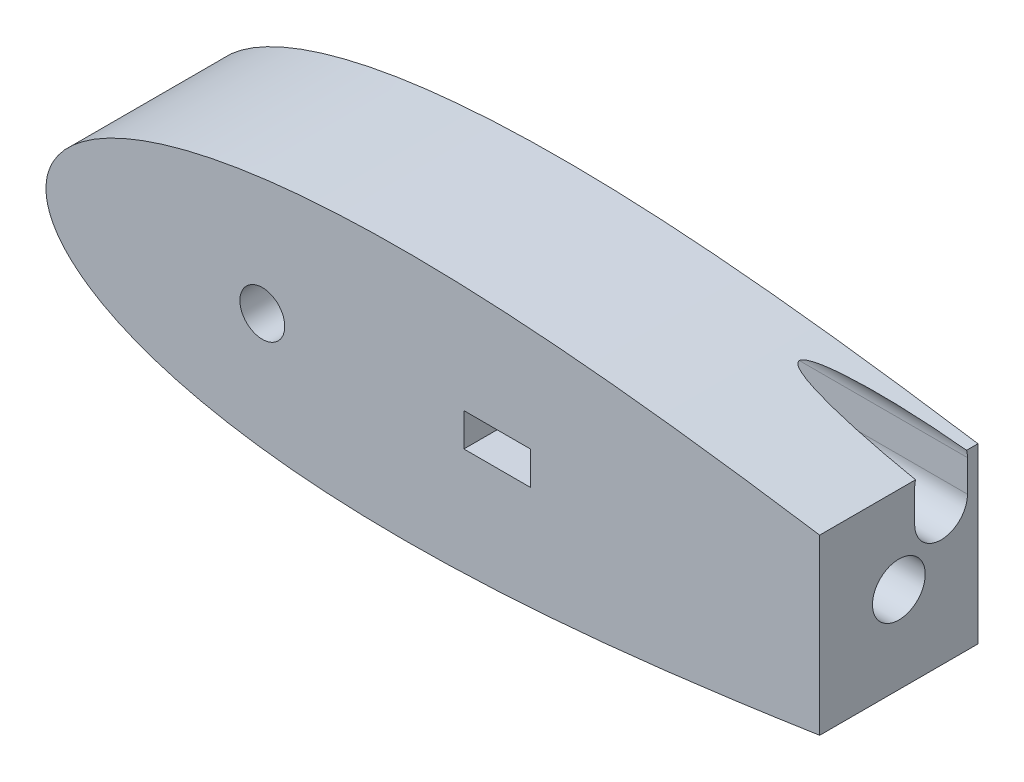
SolidWorks part; units mm, degrees
ref_plane "Front Plane" through (0, 0, 0) normal (0, 0, 1) x (1, 0, 0)
ref_plane "Top Plane" through (0, 0, 0) normal (0, 1, 0) x (1, 0, 0)
ref_plane "Right Plane" through (0, 0, 0) normal (1, 0, 0) x (0, 0, -1)
sketch "Sketch1" plane through (0, 0, 0) normal (0, 0, 1) x (1, 0, 0)
  line L0 (100, 0) -> (0, 0) construction
  line L1 (1.2169, -991.9959) -> (1.2169, 49008.0041) construction
  line L2 (93.345, 0) -> (114.935, 0) construction
  line L3 (125.634, 0) -> (131.6629, 0) construction
  line L4 (643.5991, 0) -> (643.5991, -1.016)
  line L9 (0, 0) -> (643.9668, 0)
  line L13 (460.661, 0) -> (473.361, 0)
  circle A0 centre (104.14, 0) radius 10.795 construction
  arc A1 (1.2169, -4.6585) -> (1.2169, 4.6585) centre (9.525, 0) cw
  arc A2 (641.5671, 0) -> (644.1071, 0) centre (642.8371, 0) ccw
  circle A4 centre (104.14, 0) radius 10.795
  circle A9 centre (40.64, 0) radius 12.7
  circle A14 centre (642.3793, 0) radius 1.5875 construction
  arc A15 (642.5108, -1.582) -> (642.5108, 1.582) centre (642.3793, 0) ccw
  spline S2 degree 3 poles (666.3448, -0.0547) (672.2538, 0) (666.3448, 0.0547) (662.8509, 0.2344) (656.505, 0.5436) (649.293, 1.0348) (640.4916, 1.7319) (630.4138, 2.6634) (619.0141, 3.8493) (606.375, 5.3044) (592.5439, 7.0376) (577.5855, 9.0506) (561.5643, 11.3389) (544.5497, 13.8907) (526.6141, 16.6877) (507.8326, 19.7051) (488.2827, 22.9117) (468.0444, 26.2704) (447.1994, 29.739) (425.8316, 33.2703) (404.0263, 36.8132) (381.8707, 40.3133) (359.4533, 43.7135) (336.8645, 46.9554) (314.1962, 49.9798) (291.5418, 52.7277) (268.9963, 55.1412) (246.6566, 57.1646) (224.6209, 58.7452) (202.9892, 59.8341) (181.8631, 60.3875) (161.3458, 60.367) (141.542, 59.7399) (122.5581, 58.4818) (104.5023, 56.5743) (87.485, 54.0089) (71.6197, 50.7848) (57.0237, 46.9125) (43.8205, 42.415) (32.1416, 37.3322) (22.1291, 31.7315) (13.9324, 25.7264) (7.6896, 19.5132) (3.4631, 13.4204) (1.1063, 7.9234) (0.1546, 3.5138) (-0.0622, 0) (0.1546, -3.5138) (1.1063, -7.9234) (3.4631, -13.4204) (7.6896, -19.5132) (13.9324, -25.7264) (22.1291, -31.7315) (32.1416, -37.3322) (43.8205, -42.415) (57.0237, -46.9125) (71.6197, -50.7848) (87.485, -54.0089) (104.5023, -56.5743) (122.5581, -58.4818) (141.542, -59.7399) (161.3458, -60.367) (181.8631, -60.3875) (202.9892, -59.8341) (224.6209, -58.7452) (246.6566, -57.1646) (268.9963, -55.1412) (291.5418, -52.7277) (314.1962, -49.9798) (336.8645, -46.9554) (359.4533, -43.7135) (381.8707, -40.3133) (404.0263, -36.8132) (425.8316, -33.2703) (447.1994, -29.739) (468.0444, -26.2704) (488.2827, -22.9117) (507.8326, -19.7051) (526.6141, -16.6877) (544.5497, -13.8907) (561.5643, -11.3389) (577.5855, -9.0506) (592.5439, -7.0376) (606.375, -5.3044) (619.0141, -3.8493) (630.4138, -2.6634) (640.4916, -1.7319) (649.293, -1.0348) (656.505, -0.5436) (662.8509, -0.2344) (666.3448, -0.0547) (672.2538, 0) (666.3448, 0.0547) knots -0.009667 -0.005395 -0.002168 0 0.002168 0.005395 0.009667 0.014967 0.021271 0.028553 0.036781 0.04592 0.055932 0.066773 0.078397 0.090755 0.103793 0.117456 0.131686 0.146422 0.1616 0.177156 0.193024 0.209135 0.225421 0.241812 0.258238 0.274629 0.290914 0.307025 0.322893 0.338448 0.353626 0.368361 0.38259 0.396253 0.40929 0.421647 0.43327 0.444109 0.454119 0.463255 0.471479 0.478755 0.485052 0.490344 0.49461 0.497833 0.5 0.502167 0.50539 0.509656 0.514948 0.521245 0.528521 0.536745 0.545881 0.555891 0.56673 0.578353 0.59071 0.603747 0.61741 0.631639 0.646374 0.661552 0.677107 0.692975 0.709086 0.725371 0.741762 0.758188 0.774579 0.790865 0.806976 0.822844 0.8384 0.853578 0.868314 0.882544 0.896207 0.909245 0.921603 0.933227 0.944068 0.95408 0.963219 0.971447 0.978729 0.985033 0.990333 0.994605 0.997832 1 1.002168 1.005395 1.009667 only from (670.56, 0) to (670.56, 0)
  point P2 (167.64, 0)
  point P8 (1.2169, -4.6585)
  point P10 (1.2169, 4.6585)
  point P28 (133.9182, 0)
  point P49 (130.0977, 0)
  point P59 (95.1064, 0)
  dimension "D2" = 21.59
  dimension "D3" = 1.016
  dimension "D4" = 1.27
  dimension "D8" = 25.4
  dimension "D9" = 63.5
  dimension "D10" = 3.175
  dimension "D6" = 63.5
extrude "Boss-Extrude1" add sketch "Sketch1" along normal blind 76.2 contours S2
sketch "Sketch3" plane through (0, 0, 76.2) normal (0, 0, 1) x (1, 0, 0)
  circle A0 centre (104.1392, 0) radius 10.795
  dimension "D1" = 21.59
extrude "Cut-Extrude2" cut sketch "Sketch3" against normal blind 76.2
sketch "Sketch4" plane through (0, 0, 76.2) normal (0, 0, 1) x (1, 0, 0)
sketch "Sketch6" plane through (0, 0, 0) normal (1, 0, 0) x (0, 0, -1)
  circle A0 centre (-20.32, 0) radius 6.35
  dimension "D1" = 12.7
  dimension "D2" = 20.32
extrude "Cut-Extrude3" cut sketch "Sketch6" against normal blind 0.0003 and the other way blind 53.34
sketch "Sketch7" plane through (0, 0, 0) normal (0, 0, -1) x (-1, 0, 0)
  circle A0 centre (-38.1, 0) radius 1.5875
  circle A1 centre (-50.8, 0) radius 1.5875
  dimension "D1" = 3.175
  dimension "D2" = 3.175
  dimension "D3" = 12.7
  dimension "D4" = 38.1
extrude "Cut-Extrude4" cut sketch "Sketch7" against normal blind 30.48
sketch "Sketch8" plane through (0, 0, 0) normal (0, 0, -1) x (-1, 0, 0)
  line L1 (-677.2433, 63.9901) -> (-372.4433, 63.9901)
  line L2 (-677.2433, 63.9901) -> (-677.2433, -63.0099)
  line L3 (-677.2433, -63.0099) -> (-372.4433, -63.0099)
  line L4 (-372.4433, 63.9901) -> (-372.4433, -63.0099)
  dimension "D1" = 127
  dimension "D2" = 372.4433
  dimension "D3" = 304.8
extrude "Cut-Extrude5" cut sketch "Sketch8" against normal blind 76.2
sketch "Sketch9" plane through (372.4433, 0, 0) normal (1, 0, 0) x (0, 0, -1)
  line L0 (0, -41.7363) -> (0, 41.7363) construction
  circle A0 centre (-38.1, 0) radius 12.7
  dimension "D1" = 25.4
  dimension "D2" = 38.1
extrude "Cut-Extrude6" cut sketch "Sketch9" against normal blind 101.6 contours A0
sketch "Sketch10" plane through (0, 0, 0) normal (0, 0, -1) x (-1, 0, 0)
  line L0 (-372.4433, -41.7363) -> (-372.4433, 41.7363) construction
  circle A0 centre (-343.8683, 0) radius 3.175
  circle A1 centre (-286.7183, 0) radius 3.175
  dimension "D1" = 57.15
  dimension "D2" = 28.575
  dimension "D3" = 6.35
  dimension "D4" = 6.35
extrude "Cut-Extrude7" cut sketch "Sketch10" against normal blind 57.15
sketch "Sketch11" plane through (0, 0, 0) normal (0, 0, -1) x (-1, 0, 0)
  circle A0 centre (-286.7183, 0) radius 5.08
  circle A1 centre (-343.8683, 0) radius 5.08
  dimension "D1" = 10.16
extrude "Cut-Extrude8" cut sketch "Sketch11" against normal blind 6.35
sketch "Sketch12" plane through (0, 0, 0) normal (0, 0, -1) x (-1, 0, 0)
  circle A0 centre (-38.1, 0) radius 3.175
  circle A1 centre (-50.8, 0) radius 3.175
  dimension "D1" = 6.35
  dimension "D2" = 6.35
extrude "Cut-Extrude9" cut sketch "Sketch12" against normal blind 6.35
sketch "Sketch13" plane through (372.4433, 0, 0) normal (1, 0, 0) x (0, 0, -1)
  line L0 (-17.78, 23.2323) -> (-17.78, 38.4723) construction
  line L1 (-30.48, 23.2323) -> (-30.48, 38.4723)
  line L2 (-5.08, 23.2323) -> (-5.08, 38.4723)
  line L3 (0, -41.7363) -> (0, 41.7363) construction
  line L4 (-76.2, -41.7363) -> (-76.2, 41.7363) construction
  arc A0 (-30.48, 23.2323) -> (-5.08, 23.2323) centre (-17.78, 23.2323) ccw
  arc A1 (-5.08, 38.4723) -> (-30.48, 38.4723) centre (-17.78, 38.4723) ccw
  point P2 (-17.78, 30.8523)
  dimension "D1" = 5.08
  dimension "D2" = 45.72
  dimension "D4" = 15.24
extrude "Cut-Extrude10" cut sketch "Sketch13" against normal blind 198.458
sketch "Sketch15" plane through (0, 0, 0) normal (0, 0, -1) x (-1, 0, 0)
  line L0 (-372.4433, -41.7363) -> (-372.4433, 41.7363) construction
  line L1 (-261.3613, -30.48) -> (-173.9853, -30.48)
  line L2 (-261.3613, -30.48) -> (-261.3613, 30.48)
  line L3 (-261.3613, 30.48) -> (-173.9853, 30.48)
  line L4 (-173.9853, -30.48) -> (-173.9853, 30.48)
  point P4 (0, 0)
  point P5 (0, 0)
  point P6 (0, 0)
  point P7 (0, 0)
  dimension "D1" = 87.376
  dimension "D2" = 60.96
  dimension "D3" = 111.082
extrude "Cut-Extrude11" cut sketch "Sketch15" against normal blind 33.3
sketch "Sketch17" plane through (0, 0, 33.3) normal (0, 0, -1) x (-1, 0, 0)
  line L0 (-173.9853, -30.48) -> (-173.9853, 30.48) construction
  line L1 (-233.1711, 8) -> (-201.1711, 8)
  line L2 (-233.1711, 8) -> (-233.1711, -8)
  line L3 (-233.1711, -8) -> (-201.1711, -8)
  line L4 (-201.1711, 8) -> (-201.1711, -8)
  line L5 (-173.9853, 30.48) -> (-261.3613, 30.48) construction
  dimension "D1" = 27.1858
  dimension "D2" = 32
  dimension "D3" = 16
  dimension "D4" = 22.48
extrude "Cut-Extrude12" cut sketch "Sketch17" against normal blind 50.8
sketch "Sketch18" plane through (0, 0, 33.3) normal (0, 0, -1) x (-1, 0, 0)
  line L0 (-233.1711, 8) -> (-233.1711, -8) construction
  line L1 (-201.1711, -8) -> (-201.1711, 8) construction
  circle A0 centre (-199.4711, 0) radius 1.5
  circle A1 centre (-234.8711, 0) radius 1.5
  point P6 (-233.1711, 0)
  point P7 (0, 0)
  dimension "D1" = 3
  dimension "D2" = 3
  dimension "D3" = 1.7
  dimension "D4" = 1.7
extrude "Cut-Extrude13" cut sketch "Sketch18" against normal blind 25.4
sketch "Sketch19" plane through (0, 0, 0) normal (0, 0, -1) x (-1, 0, 0)
  line L1 (-166.0439, 28.3517) -> (-112.7039, 28.3517)
  line L2 (-166.0439, 28.3517) -> (-166.0439, 49.9417)
  line L3 (-166.0439, 49.9417) -> (-112.7039, 49.9417)
  line L4 (-112.7039, 28.3517) -> (-112.7039, 49.9417)
  dimension "D1" = 53.34
  dimension "D2" = 21.59
extrude "Cut-Extrude14" cut sketch "Sketch19" against normal blind 66.04
sketch "Sketch21" plane through (0, 0, 0) normal (0, 0, -1) x (-1, 0, 0)
  line L0 (-166.0439, 28.3517) -> (-112.7039, 28.3517) construction
  line L1 (-153.594, 10.3217) -> (-125.154, 10.3217)
  line L2 (-153.594, 10.3217) -> (-153.594, 24.5417)
  line L3 (-153.594, 24.5417) -> (-125.154, 24.5417)
  line L4 (-125.154, 10.3217) -> (-125.154, 24.5417)
  point P4 (0, 0)
  point P6 (0, 0)
  dimension "D1" = 28.44
  dimension "D2" = 14.22
  dimension "D3" = 3.81
  dimension "D4" = 13.02
extrude "Cut-Extrude15" cut sketch "Sketch21" against normal blind 50.8
sketch "Sketch23" plane through (0, 0, 0) normal (0, 0, -1) x (-1, 0, 0)
  line L0 (-153.594, 24.5417) -> (-153.594, 10.3217) construction
  line L1 (-155.372, 8.2897) -> (-123.376, 8.2897)
  line L2 (-155.372, 8.2897) -> (-155.372, 26.5737)
  line L3 (-155.372, 26.5737) -> (-123.376, 26.5737)
  line L4 (-123.376, 8.2897) -> (-123.376, 26.5737)
  line L5 (-125.154, 10.3217) -> (-125.154, 24.5417) construction
  line L6 (-153.594, 10.3217) -> (-125.154, 10.3217) construction
  line L7 (-125.154, 24.5417) -> (-153.594, 24.5417) construction
  dimension "D1" = 1.778
  dimension "D2" = 1.778
  dimension "D3" = 2.032
  dimension "D4" = 2.032
extrude "Cut-Extrude16" cut sketch "Sketch23" against normal blind 10.16
sketch "Sketch24" plane through (0, 0, 0) normal (0, 0, -1) x (-1, 0, 0)
  line L7 (-165.8104, -27.5101) -> (-112.4704, -27.5101)
  line L8 (-165.8104, -27.5101) -> (-165.8104, -53.2164)
  line L9 (-165.8104, -53.2164) -> (-112.4704, -53.2164)
  line L10 (-112.4704, -27.5101) -> (-112.4704, -53.2164)
  point P1 (-112.1393, -28.2525)
extrude "Cut-Extrude17" cut sketch "Sketch24" against normal blind 50.8
